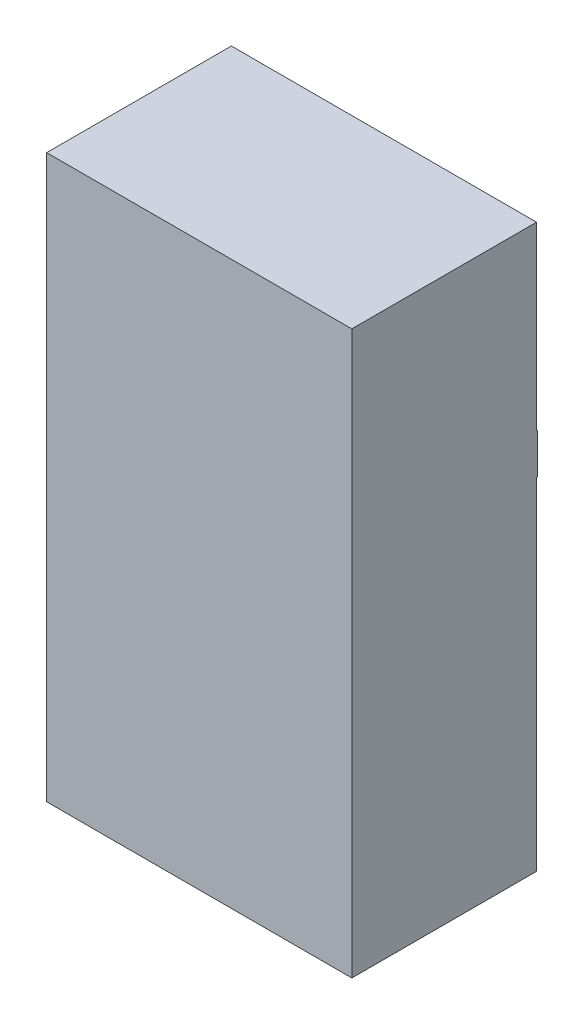
SolidWorks part; units mm, degrees
ref_plane "Front Plane" through (0, 0, 0) normal (0, 0, 1) x (1, 0, 0)
ref_plane "Top Plane" through (0, 0, 0) normal (0, 1, 0) x (1, 0, 0)
ref_plane "Right Plane" through (0, 0, 0) normal (1, 0, 0) x (0, 0, -1)
sketch "Sketch2" plane through (0, 0, 0) normal (0, 0, 1) x (1, 0, 0)
  line L1 (0, 0) -> (38, 0)
  line L2 (0, 0) -> (0, 70)
  line L3 (0, 70) -> (38, 70)
  line L4 (38, 0) -> (38, 70)
  dimension "D1" = 38
  dimension "D2" = 70
extrude "Boss-Extrude1" add sketch "Sketch2" along normal blind 23
ref_plane "Plane1" through (0, 0, 0) normal (1, 0, 0) x (0, 0, -1)
sketch "Sketch4" plane through (0, 0, 0) normal (0, -1, 0) x (1, 0, 0)
  text T0 "120V"
extrude "Cut-Extrude1" cut sketch "Sketch4" against normal blind 5
sketch "Sketch5" plane through (0, 0, 0) normal (0, 0, -1) x (-1, 0, 0)
  line L0 (-38, 0) -> (-38, 70) construction
  line L1 (-38, 47.5) -> (0, 47.5)
  line L2 (-38, 47.5) -> (-38, 42.5)
  line L3 (-38, 42.5) -> (0, 42.5)
  line L4 (0, 47.5) -> (0, 42.5)
  line L5 (0, 70) -> (0, 0) construction
  line L6 (0, 0) -> (-38, 0) construction
  dimension "D1" = 42.5
  dimension "D2" = 5
extrude "Boss-Extrude2" add sketch "Sketch5" along normal blind 0.1
